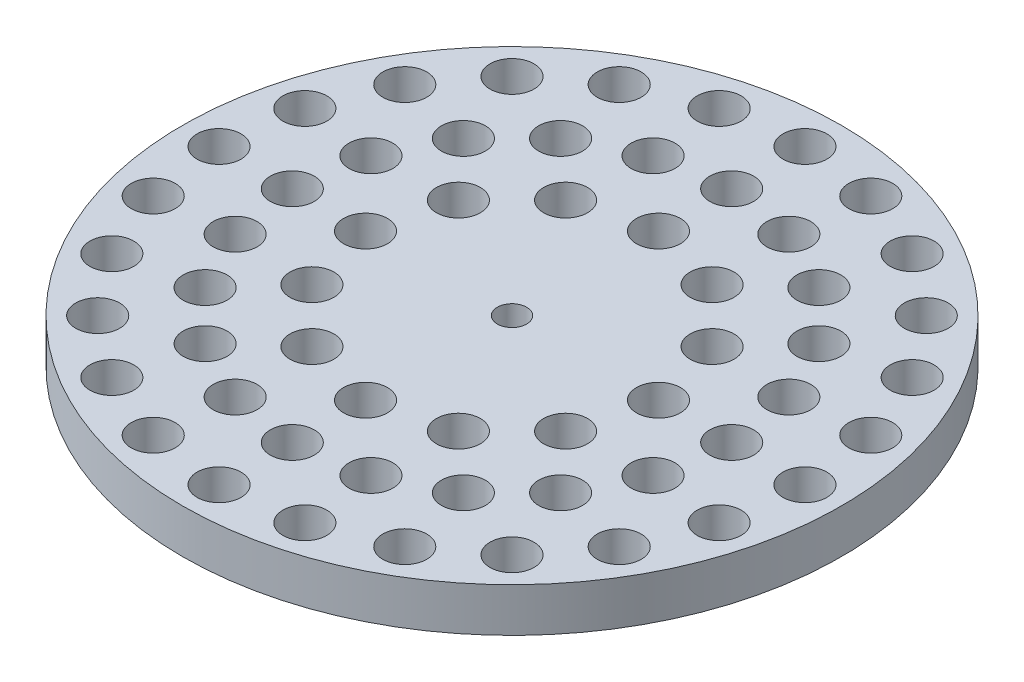
SolidWorks part; units mm, degrees
ref_plane "Plano frontal" through (0, 0, 0) normal (0, 0, 1) x (1, 0, 0)
ref_plane "Plano superior" through (0, 0, 0) normal (0, 1, 0) x (1, 0, 0)
ref_plane "Plano direito" through (0, 0, 0) normal (1, 0, 0) x (0, 0, -1)
sketch "Esboço1" plane through (0, 0, 0) normal (0, 1, 0) x (1, 0, 0)
  line L0 (0, 6.3983) -> (0, -7.8941) construction
  line L1 (-10.1044, 0) -> (9.905, 0) construction
  circle A0 centre (0, 0) radius 3.5
  circle A1 centre (0, 0) radius 5
  dimension "D1" = 7
  dimension "D2" = 10
extrude "Ressalto-extrusão1" add sketch "Esboço1" along normal blind 3.6
sketch "Esboço4" plane through (0, 3.6, 0) normal (0, 1, 0) x (1, 0, 0)
  circle A0 centre (0, 0) radius 22.5
  dimension "D1" = 45
extrude "Ressalto-extrusão2" add sketch "Esboço4" along normal blind 3
sketch "Esboço5" plane through (0, 6.6, 0) normal (0, 1, 0) x (1, 0, 0)
  line L0 (0, -29.3675) -> (0, 26.6818) construction
  line L1 (-29.4259, 0) -> (36.1986, 0) construction
  circle A0 centre (0, 0) radius 1
  circle A1 centre (0, 20) radius 1.5
  circle A2 centre (0, 15) radius 1.5
  circle A3 centre (0, 10) radius 1.5
  circle A4 centre (5, 8.6603) radius 1.5
  circle A5 centre (8.6603, 5) radius 1.5
  circle A6 centre (10, 0) radius 1.5
  circle A7 centre (8.6603, -5) radius 1.5
  circle A8 centre (5, -8.6603) radius 1.5
  circle A9 centre (0, -10) radius 1.5
  circle A10 centre (-5, -8.6603) radius 1.5
  circle A11 centre (-8.6603, -5) radius 1.5
  circle A12 centre (-10, 0) radius 1.5
  circle A13 centre (-8.6603, 5) radius 1.5
  circle A14 centre (-5, 8.6603) radius 1.5
  circle A15 centre (4.6353, 14.2658) radius 1.5
  circle A16 centre (8.8168, 12.1353) radius 1.5
  circle A17 centre (12.1353, 8.8168) radius 1.5
  circle A18 centre (14.2658, 4.6353) radius 1.5
  circle A19 centre (15, 0) radius 1.5
  circle A20 centre (14.2658, -4.6353) radius 1.5
  circle A21 centre (12.1353, -8.8168) radius 1.5
  circle A22 centre (8.8168, -12.1353) radius 1.5
  circle A23 centre (4.6353, -14.2658) radius 1.5
  circle A24 centre (0, -15) radius 1.5
  circle A25 centre (-4.6353, -14.2658) radius 1.5
  circle A26 centre (-8.8168, -12.1353) radius 1.5
  circle A27 centre (-12.1353, -8.8168) radius 1.5
  circle A28 centre (-14.2658, -4.6353) radius 1.5
  circle A29 centre (-15, 0) radius 1.5
  circle A30 centre (-14.2658, 4.6353) radius 1.5
  circle A31 centre (-12.1353, 8.8168) radius 1.5
  circle A32 centre (-8.8168, 12.1353) radius 1.5
  circle A33 centre (-4.6353, 14.2658) radius 1.5
  circle A34 centre (5.1764, 19.3185) radius 1.5
  circle A35 centre (10, 17.3205) radius 1.5
  circle A36 centre (14.1421, 14.1421) radius 1.5
  circle A37 centre (17.3205, 10) radius 1.5
  circle A38 centre (19.3185, 5.1764) radius 1.5
  circle A39 centre (20, 0) radius 1.5
  circle A40 centre (19.3185, -5.1764) radius 1.5
  circle A41 centre (17.3205, -10) radius 1.5
  circle A42 centre (14.1421, -14.1421) radius 1.5
  circle A43 centre (10, -17.3205) radius 1.5
  circle A44 centre (5.1764, -19.3185) radius 1.5
  circle A45 centre (0, -20) radius 1.5
  circle A46 centre (-5.1764, -19.3185) radius 1.5
  circle A47 centre (-10, -17.3205) radius 1.5
  circle A48 centre (-14.1421, -14.1421) radius 1.5
  circle A49 centre (-17.3205, -10) radius 1.5
  circle A50 centre (-19.3185, -5.1764) radius 1.5
  circle A51 centre (-20, 0) radius 1.5
  circle A52 centre (-19.3185, 5.1764) radius 1.5
  circle A53 centre (-17.3205, 10) radius 1.5
  circle A54 centre (-14.1421, 14.1421) radius 1.5
  circle A55 centre (-10, 17.3205) radius 1.5
  circle A56 centre (-5.1764, 19.3185) radius 1.5
  dimension "D1" = 2
  dimension "D2" = 3
  dimension "D3" = 20
  dimension "D4" = 15
  dimension "D5" = 10
  dimension "D6" = 12
  dimension "D7" = 20
  dimension "D8" = 24
extrude "Corte-extrusão2" cut sketch "Esboço5" against normal through all
